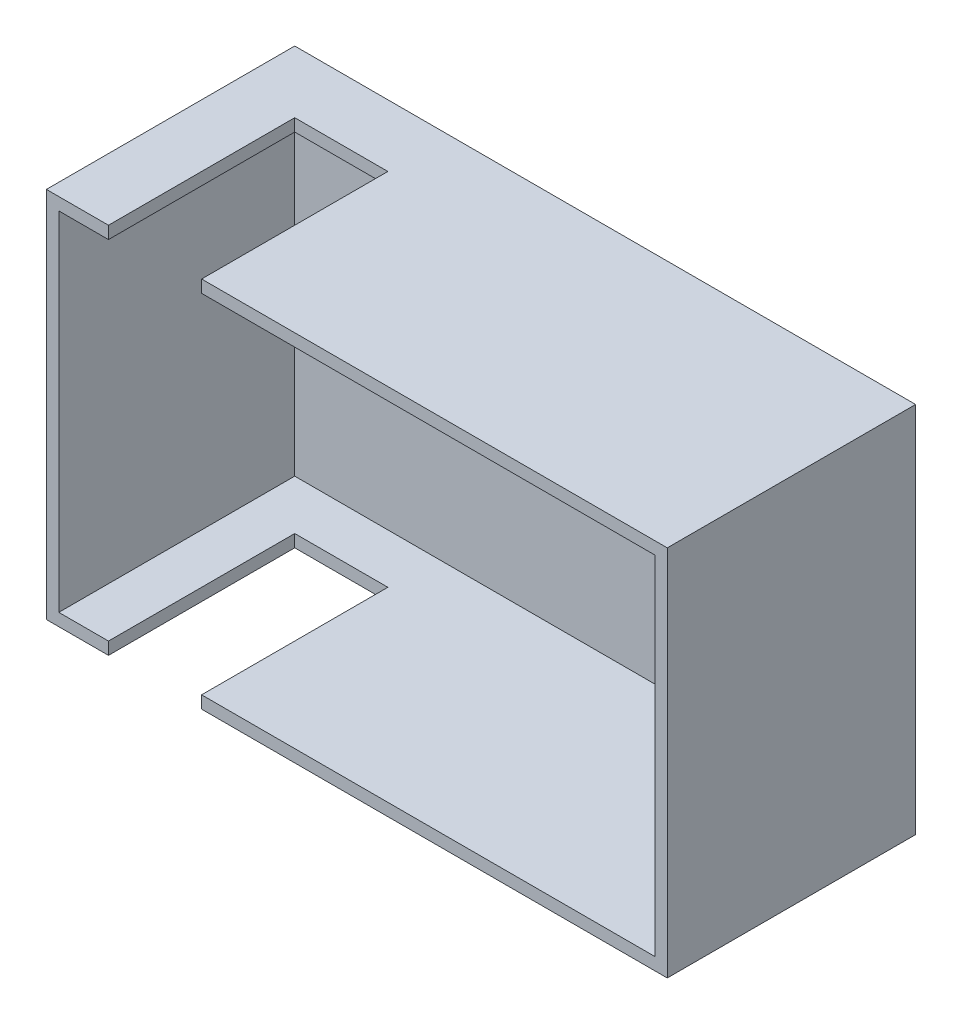
SolidWorks part; units mm, degrees
ref_plane "前基準面" through (0, 0, 0) normal (0, 0, 1) x (1, 0, 0)
ref_plane "上基準面" through (0, 0, 0) normal (0, 1, 0) x (1, 0, 0)
ref_plane "右基準面" through (0, 0, 0) normal (1, 0, 0) x (0, 0, -1)
sketch "草圖1" plane through (0, 0, 0) normal (0, 0, 1) x (1, 0, 0)
  line L1 (-50, 30) -> (50, 30)
  line L2 (-50, 30) -> (-50, -30)
  line L3 (-50, -30) -> (50, -30)
  line L4 (50, 30) -> (50, -30)
  line L5 (-50, 30) -> (50, -30) construction
  line L6 (-50, -30) -> (50, 30) construction
  point P0 (0, 0)
  dimension "D1" = 100
  dimension "D2" = 60
extrude "填料-伸長1" add sketch "草圖1" along normal blind 40
shell "薄殼1" thickness 2
sketch "草圖2" plane through (0, -30, 0) normal (0, -1, 0) x (1, 0, 0)
  line L0 (-50, 40) -> (50, 40) construction
  line L1 (-40, 40) -> (-25, 40)
  line L2 (-40, 40) -> (-40, 10)
  line L3 (-40, 10) -> (-25, 10)
  line L4 (-25, 40) -> (-25, 10)
  line L5 (-50, 40) -> (-50, 0) construction
  dimension "D1" = 15
  dimension "D2" = 30
  dimension "D3" = 10
extrude "除料-伸長1" cut sketch "草圖2" against normal blind 60
